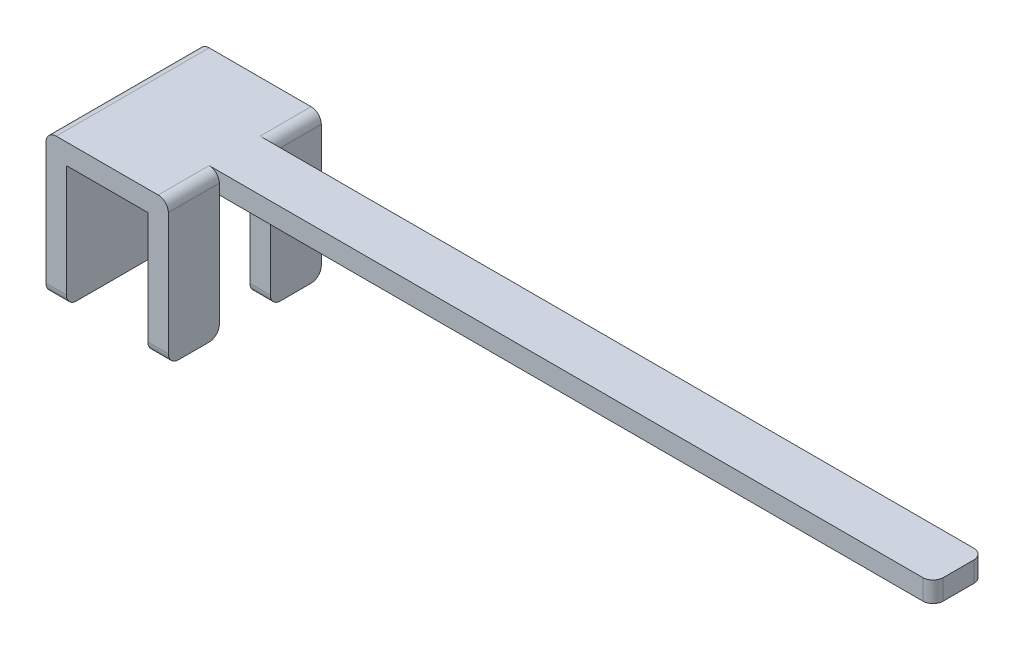
SolidWorks part; units mm, degrees
ref_plane "Front Plane" through (0, 0, 0) normal (0, 0, 1) x (1, 0, 0)
ref_plane "Top Plane" through (0, 0, 0) normal (0, 1, 0) x (1, 0, 0)
ref_plane "Right Plane" through (0, 0, 0) normal (1, 0, 0) x (0, 0, -1)
sketch "Sketch1" plane through (0, 0, 0) normal (0, 0, 1) x (1, 0, 0)
  line L0 (-0.6, 0.7) -> (-0.6, -0.6)
  line L1 (-0.4, 0.6) -> (0.4, 0.6)
  line L2 (-0.4, 0.6) -> (-0.4, -0.6)
  line L3 (0.4, -0.6) -> (0.6, -0.6)
  line L4 (0.4, 0.6) -> (0.4, -0.6)
  line L5 (-0.4, 0.6) -> (0.4, -0.6) construction
  line L6 (-0.4, -0.6) -> (0.4, 0.6) construction
  line L7 (-0.4, -0.6) -> (-0.6, -0.6)
  line L8 (0.6, 0.7) -> (0.6, -0.6)
  line L9 (-0.5, 0.8) -> (0.5, 0.8)
  line L10 (0.6, 0.8) -> (0.6, -0.8) construction
  line L11 (-0.6, 0.8) -> (0.6, 0.8) construction
  line L12 (-0.6, 0.8) -> (-0.6, -0.8) construction
  line L16 (0, 0) -> (0, -1.1809) construction
  line L20 (0.4, 0.6) -> (0.4, -0.6) construction
  line L21 (-0.4, 0.6) -> (-0.4, -0.6) construction
  line L22 (-0.4, -0.6) -> (0.4, -0.6) construction
  line L23 (-0.6, -0.8) -> (0.6, -0.8) construction
  arc A0 (0.6, 0.7) -> (0.5, 0.8) centre (0.5, 0.7) ccw
  arc A1 (-0.6, 0.7) -> (-0.5, 0.8) centre (-0.5, 0.7) cw
  point P0 (0, 0)
  point P18 (0.6846, -0.5466)
  point P19 (0.5796, -0.3803)
  dimension "D1" = 1.2
  dimension "D2" = 0.8
  dimension "D3" = 0.2
extrude "Boss-Extrude1" add sketch "Sketch1" along normal blind 1.5
sketch "Sketch5" plane through (0, 0, 1.5) normal (0, 0, 1) x (1, 0, 0)
  line L0 (0.5, 0.8) -> (-0.5, 0.8) construction
  line L1 (0, 0.8) -> (7.6, 0.8)
  line L2 (0, 0.8) -> (0, 0.6)
  line L3 (0, 0.6) -> (7.6, 0.6)
  line L4 (7.6, 0.8) -> (7.6, 0.6)
  line L5 (0.6, -0.6) -> (0.6, 0.7) construction
  dimension "D1" = 7
extrude "Boss-Extrude3" add sketch "Sketch5" along normal blind 0.5 from offset 1 offset against normal yes
sketch "Sketch6" plane through (0.6, 0, 0) normal (1, 0, 0) x (0, 0, -1)
  line L0 (-1.5, -0.6) -> (0, -0.6) construction
  line L1 (-1, 0.6) -> (-0.5, 0.6)
  line L2 (-1, 0.6) -> (-1, -0.6)
  line L3 (-1, -0.6) -> (-0.5, -0.6)
  line L4 (-0.5, 0.6) -> (-0.5, -0.6)
extrude "Cut-Extrude2" cut sketch "Sketch6" against normal blind 0.5
fillet "Fillet2" radius 0.1 8 edges at (7.6, 0.7, 1) (7.6, 0.7, 0.5) (-0.5, -0.6, 0) (0.5, -0.6, 0) (0.5, -0.6, 0.5) (0.5, -0.6, 1) (0.5, -0.6, 1.5) (-0.5, -0.6, 1.5)
